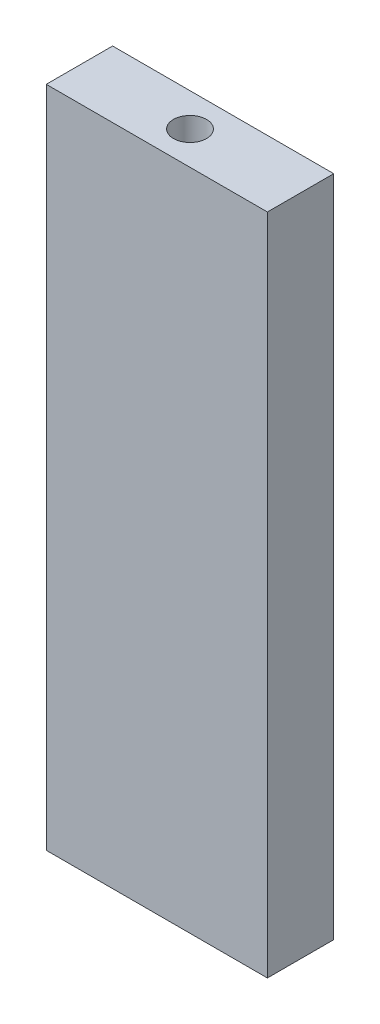
SolidWorks part; units mm, degrees
ref_plane "Front Plane" through (0, 0, 0) normal (0, 0, 1) x (1, 0, 0)
ref_plane "Top Plane" through (0, 0, 0) normal (0, 1, 0) x (1, 0, 0)
ref_plane "Right Plane" through (0, 0, 0) normal (1, 0, 0) x (0, 0, -1)
sketch "Sketch1" plane through (0, 0, 0) normal (0, 0, 1) x (1, 0, 0)
  line L1 (-10, 30) -> (10, 30)
  line L2 (-10, 30) -> (-10, -30)
  line L3 (-10, -30) -> (10, -30)
  line L4 (10, 30) -> (10, -30)
  line L5 (-10, 30) -> (10, -30) construction
  line L6 (-10, -30) -> (10, 30) construction
  point P0 (0, 0)
  dimension "D1" = 20
  dimension "D2" = 60
extrude "Boss-Extrude1" add sketch "Sketch1" along normal blind 6
sketch "Sketch2" plane through (0, 30, 0) normal (0, 1, 0) x (1, 0, 0)
  line L0 (-10, 0) -> (10, -6) construction
  circle A0 centre (0, -3) radius 1.5
  dimension "D1" = 3
extrude "Cut-Extrude1" cut sketch "Sketch2" against normal blind 10
mirror "Mirror1" about plane through (0, 0, 0) normal (0, 1, 0) of "Cut-Extrude1"
